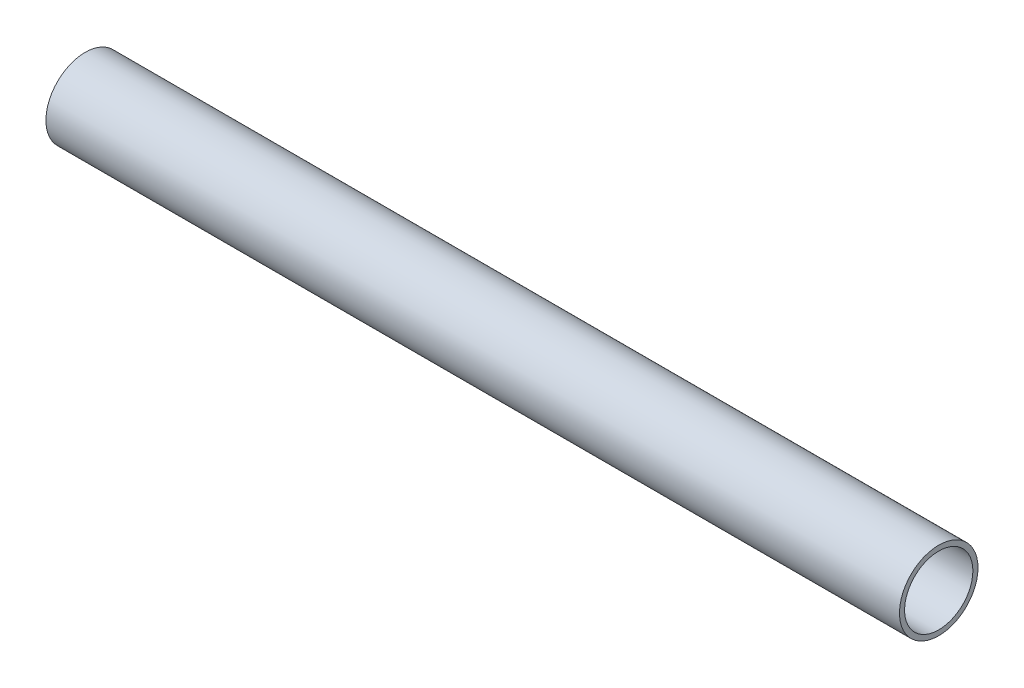
SolidWorks part; units mm, degrees
ref_plane "Front Plane" through (0, 0, 0) normal (0, 0, 1) x (1, 0, 0)
ref_plane "Top Plane" through (0, 0, 0) normal (0, 1, 0) x (1, 0, 0)
ref_plane "Right Plane" through (0, 0, 0) normal (1, 0, 0) x (0, 0, -1)
sketch "Sketch1" plane through (0, 0, 0) normal (1, 0, 0) x (0, 0, -1)
  circle A0 centre (0, 0) radius 11.5
  circle A1 centre (0, 0) radius 10
  dimension "D1" = 20
  dimension "D2" = 23
extrude "Boss-Extrude2" add sketch "Sketch1" along normal blind 250
